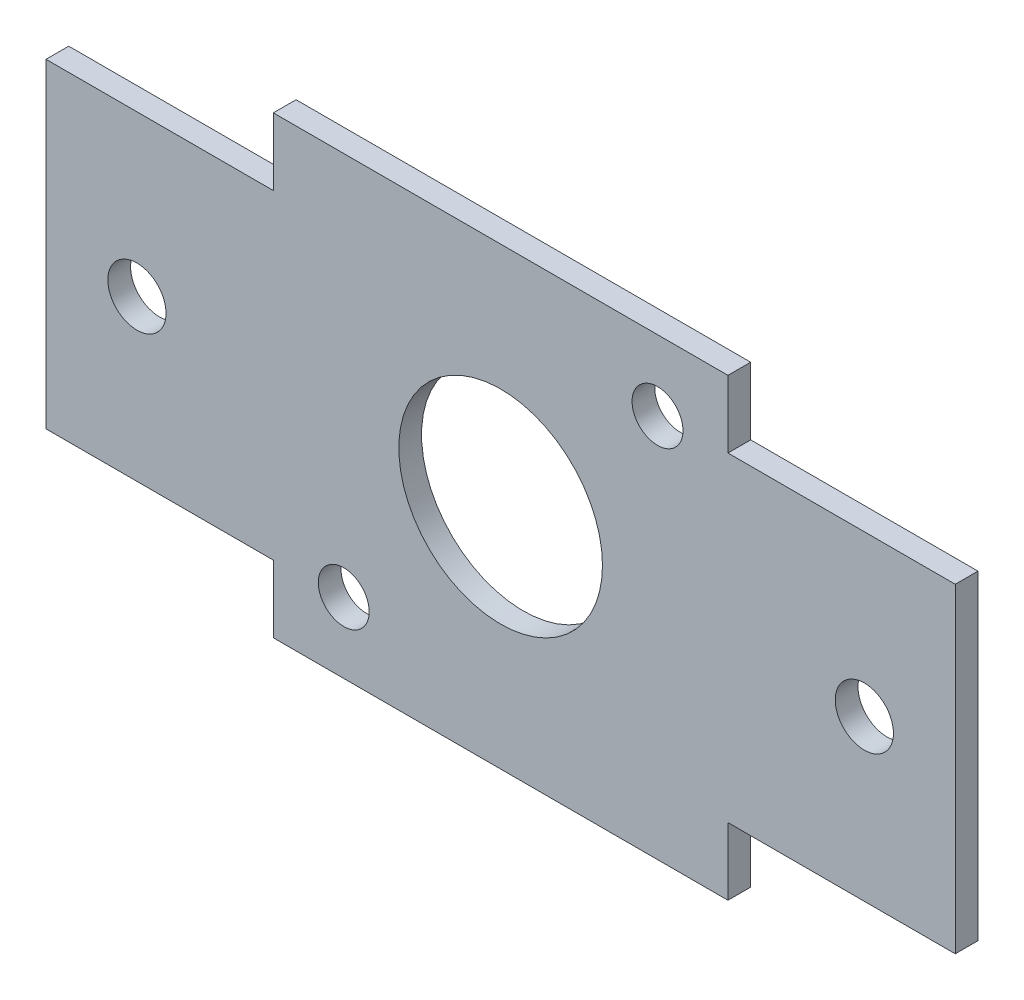
SolidWorks part; units mm, degrees
ref_plane "Front" through (0, 0, 0) normal (0, 0, 1) x (1, 0, 0)
ref_plane "Top" through (0, 0, 0) normal (0, 1, 0) x (1, 0, 0)
ref_plane "Right" through (0, 0, 0) normal (1, 0, 0) x (0, 0, -1)
sketch "Sketch1" plane through (0, 0, 0) normal (0, 0, 1) x (1, 0, 0)
  line L0 (31.75, 0) -> (15.875, 0) construction
  line L1 (-15.875, -15.875) -> (15.875, -15.875)
  line L2 (-15.875, -15.875) -> (-15.875, 15.875)
  line L3 (-15.875, 15.875) -> (15.875, 15.875)
  line L4 (15.875, -15.875) -> (15.875, 15.875)
  line L5 (-15.875, -15.875) -> (15.875, 15.875) construction
  line L6 (-15.875, 15.875) -> (15.875, -15.875) construction
  line L7 (15.875, -11.176) -> (31.75, -11.176)
  line L8 (15.875, -11.176) -> (15.875, 11.176)
  line L9 (15.875, 11.176) -> (31.75, 11.176)
  line L10 (31.75, -11.176) -> (31.75, 11.176)
  line L11 (-15.875, -11.176) -> (-31.75, -11.176)
  line L12 (-15.875, -11.176) -> (-15.875, 11.176)
  line L13 (-15.875, 11.176) -> (-31.75, 11.176)
  line L14 (-31.75, -11.176) -> (-31.75, 11.176)
  line L15 (-15.875, 0) -> (-31.75, 0) construction
  circle A0 centre (10.9559, 10.9559) radius 1.778
  circle A1 centre (-10.9559, 10.9559) radius 1.778 construction
  circle A2 centre (-10.9559, -10.9559) radius 1.778
  circle A3 centre (10.9559, -10.9559) radius 1.778 construction
  circle A4 centre (0, 0) radius 7.112
  circle A5 centre (-25.4, 0) radius 2.032
  circle A6 centre (25.4, 0) radius 2.032
  point P0 (0, 0)
  dimension "D2" = 14.224
  dimension "D3" = 3.556
  dimension "D6" = 4.064
  dimension "D1" = 31.75
  dimension "D4" = 15.494
  dimension "D5" = 25.4
  dimension "D7" = 31.75
  dimension "D8" = 22.352
  dimension "D9" = 25.4
extrude "Boss-Extrude1" add sketch "Sketch1" along normal blind 1.5875 contours L14 L11 L2 L13 A5 | L1 L4 L3 L2 A4 A2 A0 | L7 L10 L9 L4 A6
equation "\"D9@Sketch1\"=\"D5@Sketch1\""
